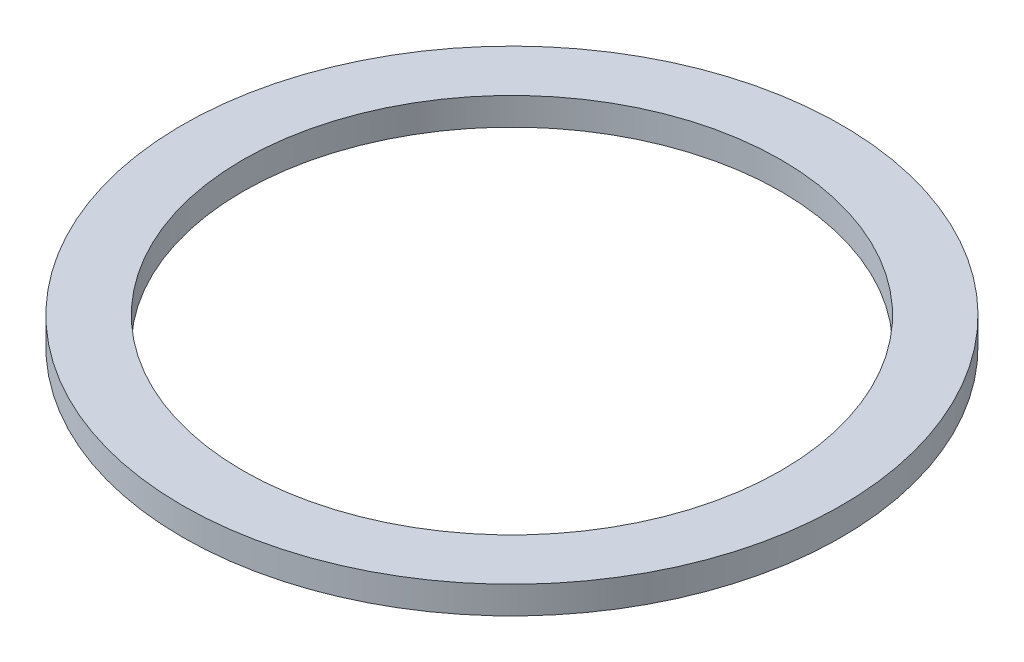
SolidWorks part; units mm, degrees
ref_plane "Front Plane" through (0, 0, 0) normal (0, 0, 1) x (1, 0, 0)
ref_plane "Top Plane" through (0, 0, 0) normal (0, 1, 0) x (1, 0, 0)
ref_plane "Right Plane" through (0, 0, 0) normal (1, 0, 0) x (0, 0, -1)
sketch "Sketch1" plane through (0, 0, 0) normal (0, 1, 0) x (1, 0, 0)
  circle A0 centre (0, 0) radius 120
  circle A1 centre (0, 0) radius 98
  dimension "D1" = 196
  dimension "D2" = 240
extrude "Boss-Extrude1" add sketch "Sketch1" along normal blind 10
sketch "Sketch2" plane through (0, 0, 0) normal (0, 0, 1) x (1, 0, 0)
  line L0 (-120, 0) -> (120, 0) construction
  circle A0 centre (110, -1) radius 3
  dimension "D1" = 6
  dimension "D2" = 1
  dimension "D3" = 110
sketch3d "3DSketch1"
  line L0 (0, 0, 0) -> (0, 23.4866, 0) construction
revolve "Cut-Revolve1" cut sketch "Sketch2" angle 360 about L0
